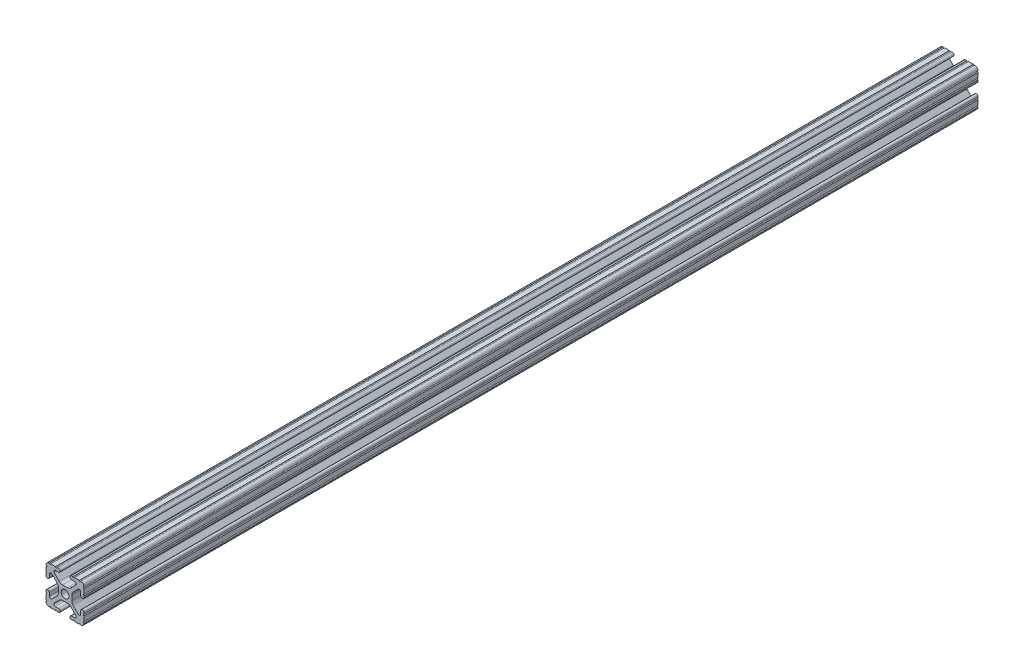
SolidWorks part; units mm, degrees
ref_plane "Front Plane" through (0, 0, 0) normal (0, 0, 1) x (1, 0, 0)
ref_plane "Top Plane" through (0, 0, 0) normal (0, 1, 0) x (1, 0, 0)
ref_plane "Right Plane" through (0, 0, 0) normal (1, 0, 0) x (0, 0, -1)
ref_plane "Plane1" through (0, 0, 0) normal (0, 0, 1) x (1, 0, 0)
sketch "Sketch1" plane through (0, 0, 0) normal (0, 0, 1) x (1, 0, 0)
  line L0 (-12.7, 9.5504) -> (-12.7, 6.3331)
  line L1 (-12.7, 5.3171) -> (-12.7, 4.3434)
  line L2 (-10.4902, 4.3434) -> (-10.4902, 6.4748)
  line L3 (-8.7558, 7.1932) -> (-5.4257, 3.8632)
  line L4 (-4.4958, 1.6181) -> (-4.4958, -1.6181)
  line L5 (-5.4257, -3.8632) -> (-8.7558, -7.1932)
  line L6 (-10.4902, -6.4748) -> (-10.4902, -4.3434)
  line L7 (-12.7, -4.3434) -> (-12.7, -5.3171)
  line L8 (-12.7, -6.3331) -> (-12.7, -9.5504)
  line L9 (-9.5504, -12.7) -> (-6.3331, -12.7)
  line L10 (-5.3171, -12.7) -> (-4.3434, -12.7)
  line L11 (-4.3434, -10.4902) -> (-6.4748, -10.4902)
  line L12 (-7.1932, -8.7558) -> (-3.8632, -5.4257)
  line L13 (-1.6181, -4.4958) -> (1.6181, -4.4958)
  line L14 (3.8632, -5.4257) -> (7.1932, -8.7558)
  line L15 (6.4748, -10.4902) -> (4.3434, -10.4902)
  line L16 (4.3434, -12.7) -> (5.3171, -12.7)
  line L17 (6.3331, -12.7) -> (9.5504, -12.7)
  line L18 (12.7, -9.5504) -> (12.7, -6.3331)
  line L19 (12.7, -5.3171) -> (12.7, -4.3434)
  line L20 (10.4902, -4.3434) -> (10.4902, -6.4748)
  line L21 (8.7558, -7.1932) -> (5.4257, -3.8632)
  line L22 (4.4958, -1.6181) -> (4.4958, 1.6181)
  line L23 (5.4257, 3.8632) -> (8.7558, 7.1932)
  line L24 (10.4902, 6.4748) -> (10.4902, 4.3434)
  line L25 (12.7, 4.3434) -> (12.7, 5.3171)
  line L26 (12.7, 6.3331) -> (12.7, 9.5504)
  line L27 (9.5504, 12.7) -> (6.3331, 12.7)
  line L28 (5.3171, 12.7) -> (4.3434, 12.7)
  line L29 (4.3434, 10.4902) -> (6.4748, 10.4902)
  line L30 (7.1932, 8.7558) -> (3.8632, 5.4257)
  line L31 (1.6181, 4.4958) -> (-1.6181, 4.4958)
  line L32 (-3.8632, 5.4257) -> (-7.1932, 8.7558)
  line L33 (-6.4748, 10.4902) -> (-4.3434, 10.4902)
  line L34 (-4.3434, 12.7) -> (-5.3171, 12.7)
  line L35 (-6.3331, 12.7) -> (-9.5504, 12.7)
  arc A0 (-12.7, 6.3331) -> (-12.7, 5.3171) centre (-12.7, 5.8251) cw
  arc A1 (-12.7, 4.3434) -> (-10.4902, 4.3434) centre (-11.5951, 4.3434) ccw
  arc A2 (-10.4902, 6.4748) -> (-8.7558, 7.1932) centre (-9.4742, 6.4748) cw
  arc A3 (-5.4257, 3.8632) -> (-4.4958, 1.6181) centre (-7.6708, 1.6181) cw
  arc A4 (-4.4958, -1.6181) -> (-5.4257, -3.8632) centre (-7.6708, -1.6181) cw
  arc A5 (-8.7558, -7.1932) -> (-10.4902, -6.4748) centre (-9.4742, -6.4748) cw
  arc A6 (-10.4902, -4.3434) -> (-12.7, -4.3434) centre (-11.5951, -4.3434) ccw
  arc A7 (-12.7, -5.3171) -> (-12.7, -6.3331) centre (-12.7, -5.8251) cw
  arc A8 (-12.7, -9.5504) -> (-12.6998, -10.5664) centre (-12.7, -10.0584) cw
  arc A9 (-12.6998, -10.5664) -> (-10.5664, -12.6998) centre (-10.5918, -10.5918) ccw
  arc A10 (-10.5664, -12.6998) -> (-9.5504, -12.7) centre (-10.0584, -12.7) cw
  arc A11 (-6.3331, -12.7) -> (-5.3171, -12.7) centre (-5.8251, -12.7) cw
  arc A12 (-4.3434, -12.7) -> (-4.3434, -10.4902) centre (-4.3434, -11.5951) ccw
  arc A13 (-6.4748, -10.4902) -> (-7.1932, -8.7558) centre (-6.4748, -9.4742) cw
  arc A14 (-3.8632, -5.4257) -> (-1.6181, -4.4958) centre (-1.6181, -7.6708) cw
  arc A15 (1.6181, -4.4958) -> (3.8632, -5.4257) centre (1.6181, -7.6708) cw
  arc A16 (7.1932, -8.7558) -> (6.4748, -10.4902) centre (6.4748, -9.4742) cw
  arc A17 (4.3434, -10.4902) -> (4.3434, -12.7) centre (4.3434, -11.5951) ccw
  arc A18 (5.3171, -12.7) -> (6.3331, -12.7) centre (5.8251, -12.7) cw
  arc A19 (9.5504, -12.7) -> (10.5664, -12.6998) centre (10.0584, -12.7) cw
  arc A20 (10.5664, -12.6998) -> (12.6998, -10.5664) centre (10.5918, -10.5918) ccw
  arc A21 (12.6998, -10.5664) -> (12.7, -9.5504) centre (12.7, -10.0584) cw
  arc A22 (12.7, -6.3331) -> (12.7, -5.3171) centre (12.7, -5.8251) cw
  arc A23 (12.7, -4.3434) -> (10.4902, -4.3434) centre (11.5951, -4.3434) ccw
  arc A24 (10.4902, -6.4748) -> (8.7558, -7.1932) centre (9.4742, -6.4748) cw
  arc A25 (5.4257, -3.8632) -> (4.4958, -1.6181) centre (7.6708, -1.6181) cw
  arc A26 (4.4958, 1.6181) -> (5.4257, 3.8632) centre (7.6708, 1.6181) cw
  arc A27 (8.7558, 7.1932) -> (10.4902, 6.4748) centre (9.4742, 6.4748) cw
  arc A28 (10.4902, 4.3434) -> (12.7, 4.3434) centre (11.5951, 4.3434) ccw
  arc A29 (12.7, 5.3171) -> (12.7, 6.3331) centre (12.7, 5.8251) cw
  arc A30 (12.7, 9.5504) -> (12.6998, 10.5664) centre (12.7, 10.0584) cw
  arc A31 (12.6998, 10.5664) -> (10.5664, 12.6998) centre (10.5918, 10.5918) ccw
  arc A32 (10.5664, 12.6998) -> (9.5504, 12.7) centre (10.0584, 12.7) cw
  arc A33 (6.3331, 12.7) -> (5.3171, 12.7) centre (5.8251, 12.7) cw
  arc A34 (4.3434, 12.7) -> (4.3434, 10.4902) centre (4.3434, 11.5951) ccw
  arc A35 (6.4748, 10.4902) -> (7.1932, 8.7558) centre (6.4748, 9.4742) cw
  arc A36 (3.8632, 5.4257) -> (1.6181, 4.4958) centre (1.6181, 7.6708) cw
  arc A37 (-1.6181, 4.4958) -> (-3.8632, 5.4257) centre (-1.6181, 7.6708) cw
  arc A38 (-7.1932, 8.7558) -> (-6.4748, 10.4902) centre (-6.4748, 9.4742) cw
  arc A39 (-4.3434, 10.4902) -> (-4.3434, 12.7) centre (-4.3434, 11.5951) ccw
  arc A40 (-5.3171, 12.7) -> (-6.3331, 12.7) centre (-5.8251, 12.7) cw
  arc A41 (-9.5504, 12.7) -> (-10.5664, 12.6998) centre (-10.0584, 12.7) cw
  arc A42 (-10.5664, 12.6998) -> (-12.6998, 10.5664) centre (-10.5918, 10.5918) ccw
  arc A43 (-12.6998, 10.5664) -> (-12.7, 9.5504) centre (-12.7, 10.0584) cw
  circle A44 centre (0, 0) radius 2.6035
extrude "Boss-Extrude1" add sketch "Sketch1" against normal blind 596.9
